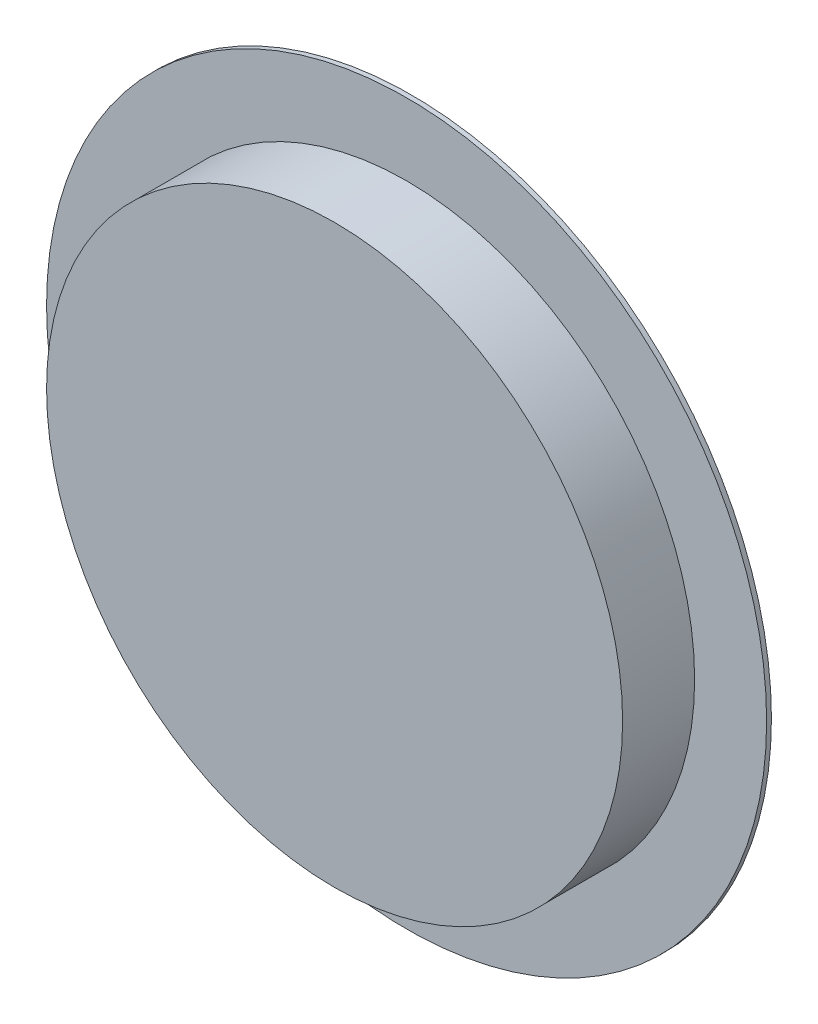
SolidWorks part; units mm, degrees
ref_plane "Front Plane" through (0, 0, 0) normal (0, 0, 1) x (1, 0, 0)
ref_plane "Top Plane" through (0, 0, 0) normal (0, 1, 0) x (1, 0, 0)
ref_plane "Right Plane" through (0, 0, 0) normal (1, 0, 0) x (0, 0, -1)
sketch "Sketch1" plane through (0, 0, 0) normal (0, 0, 1) x (1, 0, 0)
  circle A0 centre (0, 0) radius 75
  dimension "D1" = 150
extrude "Boss-Extrude1" add sketch "Sketch1" along normal blind 1
sketch "Sketch2" plane through (0, 0, 1) normal (0, 0, 1) x (1, 0, 0)
  circle A0 centre (0, 0) radius 60
  dimension "D1" = 120
extrude "Boss-Extrude2" add sketch "Sketch2" along normal blind 15
